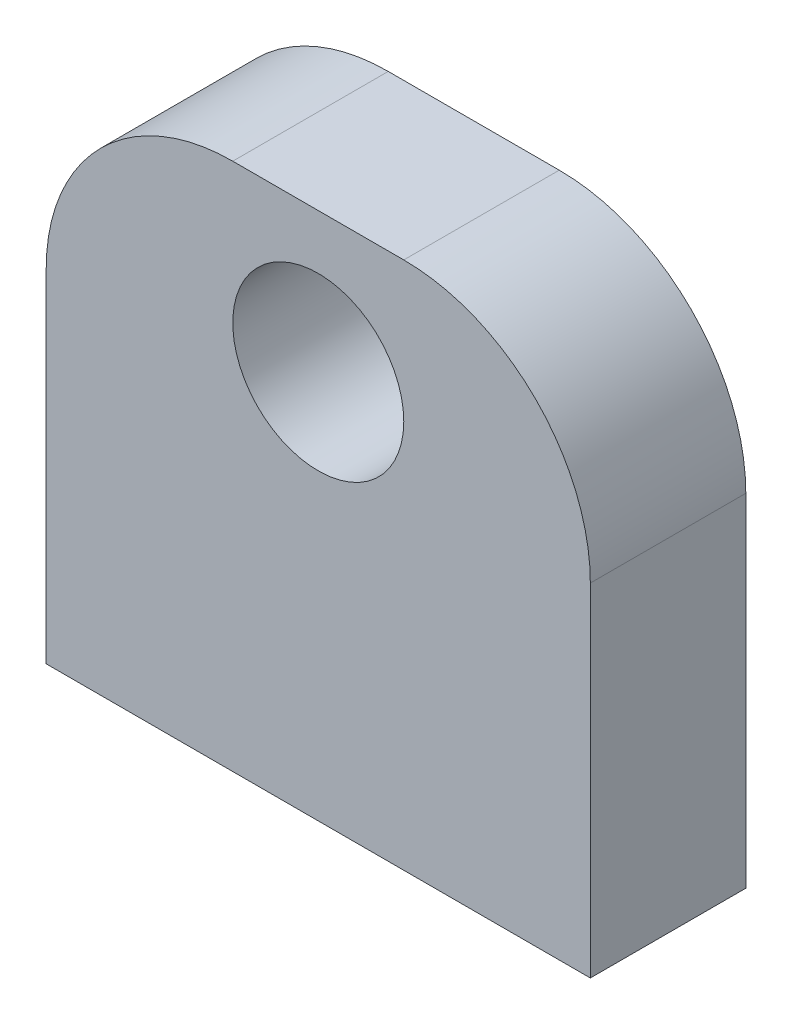
SolidWorks part; units mm, degrees
ref_plane "Front Plane" through (0, 0, 0) normal (0, 0, 1) x (1, 0, 0)
ref_plane "Top Plane" through (0, 0, 0) normal (0, 1, 0) x (1, 0, 0)
ref_plane "Right Plane" through (0, 0, 0) normal (1, 0, 0) x (0, 0, -1)
sketch "Sketch1" plane through (0, 0, 0) normal (0, 1, 0) x (1, 0, 0)
  line L1 (-16.3353, 9.1448) -> (18.6647, 9.1448)
  line L2 (-16.3353, 9.1448) -> (-16.3353, -0.8552)
  line L3 (-16.3353, -0.8552) -> (18.6647, -0.8552)
  line L4 (18.6647, 9.1448) -> (18.6647, -0.8552)
  dimension "D1" = 35
  dimension "D2" = 10
extrude "Boss-Extrude1" add sketch "Sketch1" along normal blind 34
sketch "Sketch2" plane through (0, 0, 0.8552) normal (0, 0, 1) x (1, 0, 0)
  line L0 (18.6647, 34) -> (18.6647, 0) construction
  line L2 (-16.3353, 34) -> (18.6647, 34) construction
  circle A0 centre (1.1647, 25) radius 5.5
  dimension "D1" = 17.5
  dimension "D2" = 9
extrude "Cut-Extrude1" cut sketch "Sketch2" against normal through all
sketch "Sketch3" plane through (0, 0, 0) normal (0, -1, 0) x (1, 0, 0)
  line L0 (18.6647, -9.1448) -> (-16.3353, -9.1448) construction
  line L1 (-16.3353, -9.1448) -> (-16.3353, 0.8552) construction
  line L2 (18.6647, 0.8552) -> (18.6647, -9.1448) construction
  circle A0 centre (-8.3353, -4.1448) radius 1.75
  circle A1 centre (10.6647, -4.1448) radius 1.75
  point P4 (-16.3353, -4.1448)
  dimension "D1" = 5
  dimension "D3" = 5
  dimension "D2" = 8
  dimension "D4" = 8
extrude "Cut-Extrude2" cut sketch "Sketch3" against normal blind 10
fillet "Fillet1" radius 12 2 edges at (18.6647, 34, -4.1448) (-16.3353, 34, -4.1448)
